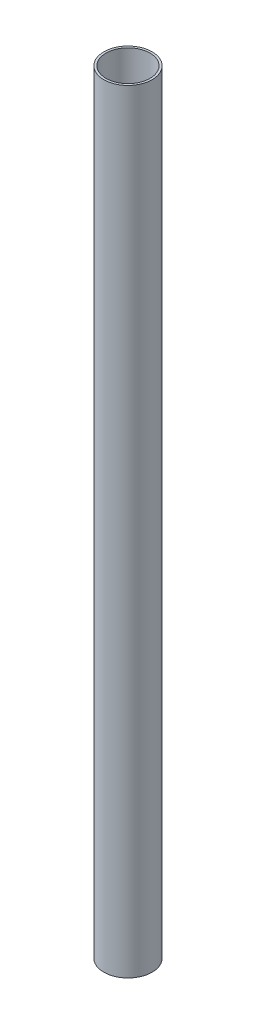
SolidWorks part; units mm, degrees
ref_plane "Front Plane" through (0, 0, 0) normal (0, 0, 1) x (1, 0, 0)
ref_plane "Top Plane" through (0, 0, 0) normal (0, 1, 0) x (1, 0, 0)
ref_plane "Right Plane" through (0, 0, 0) normal (1, 0, 0) x (0, 0, -1)
sketch "Sketch1" plane through (0, 0, 0) normal (0, 1, 0) x (1, 0, 0)
  circle A0 centre (0, 0) radius 7.9375
  circle A1 centre (0, 0) radius 7.2263
  dimension "D1" = 15.875
  dimension "D2" = 14.4526
extrude "Boss-Extrude1" add sketch "Sketch1" along normal blind 254
